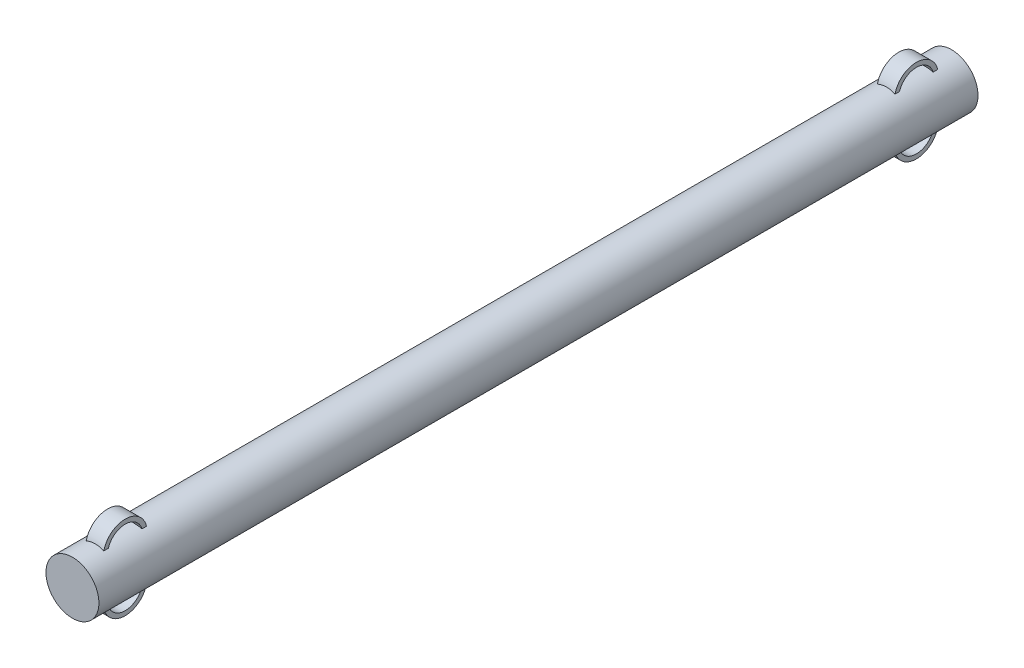
SolidWorks part; units mm, degrees
ref_plane "Alzado" through (0, 0, 0) normal (0, 0, 1) x (1, 0, 0)
ref_plane "Planta" through (0, 0, 0) normal (0, 1, 0) x (1, 0, 0)
ref_plane "Vista lateral" through (0, 0, 0) normal (1, 0, 0) x (0, 0, -1)
sketch "Sketch1" plane through (0, 0, 0) normal (0, 0, 1) x (1, 0, 0)
  circle A0 centre (0, 0) radius 1.5303
  dimension "D1" = 3.0607
extrude "Boss-Extrude1" add sketch "Sketch1" along normal blind 50.8
sketch "Sketch2" plane through (0, 0, 0) normal (1, 0, 0) x (0, 0, -1)
  line L0 (-50.8, 1.1494) -> (-49.276, 1.1494)
  line L1 (-50.8, 1.5304) -> (-50.8, -1.5304) construction
  line L2 (-47.244, 1.1494) -> (-46.99, 1.1494)
  arc A0 (-47.244, 1.1494) -> (-49.276, 1.1494) centre (-48.26, 1.1494) ccw
  arc A1 (-46.99, 1.1494) -> (-49.53, 1.1494) centre (-48.26, 1.1494) ccw
  dimension "D2" = 2.032
  dimension "D3" = 2.54
  dimension "D1" = 2.54
  dimension "D4" = 0.381
extrude "Boss-Extrude2" add sketch "Sketch2" along normal mid plane 1.016 contours L2 A1 L0 A0
mirror "Mirror1" about plane through (0, 0, 0) normal (0, 1, 0) of "Boss-Extrude2"
ref_plane "Plane1" through (0, 0, 25.4) normal (0, 0, -1) x (-1, 0, 0)
mirror "Mirror2" about plane through (0, 0, 25.4) normal (0, 0, -1) of "Mirror1", "Boss-Extrude2"
